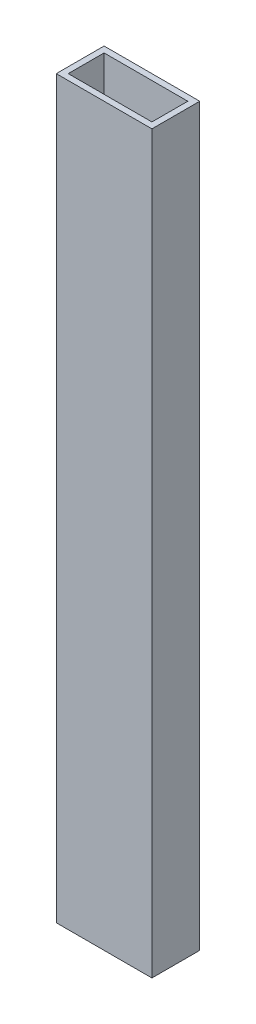
SolidWorks part; units mm, degrees
ref_plane "Front Plane" through (0, 0, 0) normal (0, 0, 1) x (1, 0, 0)
ref_plane "Top Plane" through (0, 0, 0) normal (0, 1, 0) x (1, 0, 0)
ref_plane "Right Plane" through (0, 0, 0) normal (1, 0, 0) x (0, 0, -1)
sketch "Sketch1" plane through (0, 0, 0) normal (0, 1, 0) x (1, 0, 0)
  line L1 (0, 0) -> (50.8, 0)
  line L2 (0, 0) -> (0, 25.4)
  line L3 (0, 25.4) -> (50.8, 25.4)
  line L4 (50.8, 0) -> (50.8, 25.4)
  line L5 (3.175, 22.225) -> (47.625, 22.225)
  line L6 (3.175, 22.225) -> (3.175, 3.175)
  line L7 (3.175, 3.175) -> (47.625, 3.175)
  line L8 (47.625, 22.225) -> (47.625, 3.175)
  dimension "D1" = 3.175
  dimension "D2" = 3.175
  dimension "D3" = 3.175
  dimension "D4" = 3.175
  dimension "D5" = 50.8
  dimension "D6" = 25.4
extrude "Boss-Extrude1" add sketch "Sketch1" along normal blind 390.525
